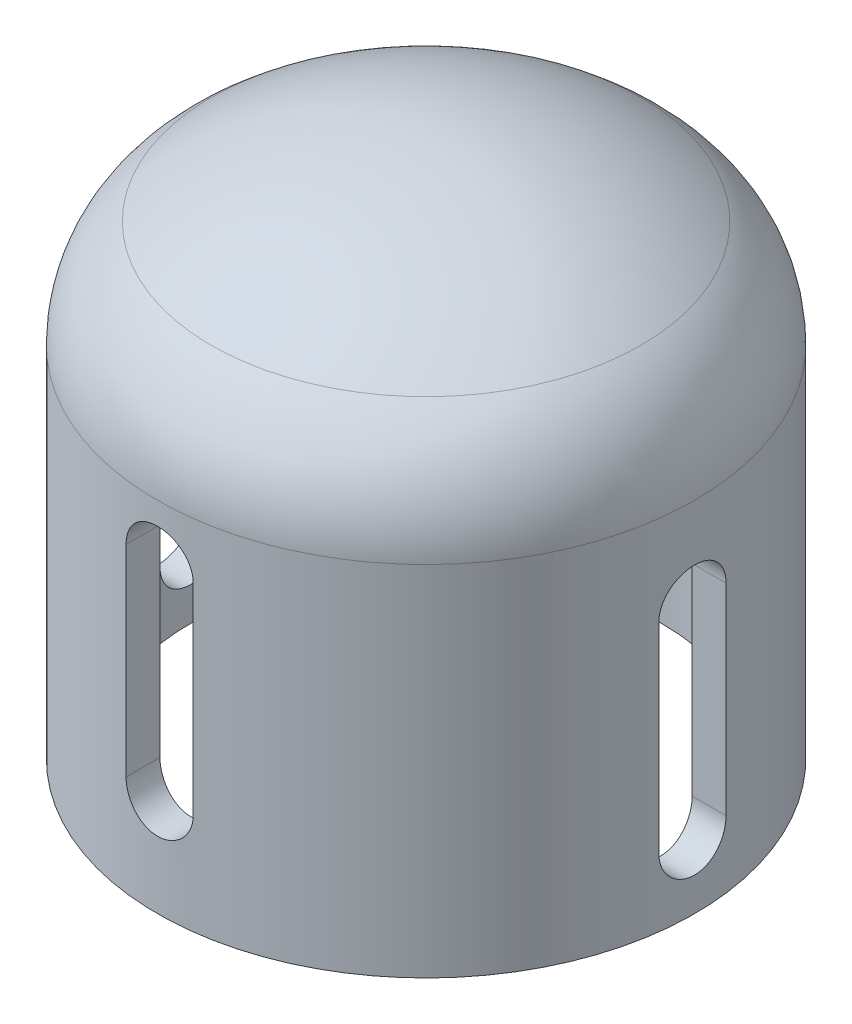
SolidWorks part; units mm, degrees
material "Acciaio inossidabile al cromo"
ref_plane "Piano frontale" through (0, 0, 0) normal (0, 0, 1) x (1, 0, 0)
ref_plane "Piano superiore" through (0, 0, 0) normal (0, 1, 0) x (1, 0, 0)
ref_plane "Piano destro" through (0, 0, 0) normal (1, 0, 0) x (0, 0, -1)
sketch "Schizzo1" plane through (0, 0, 0) normal (0, 0, 1) x (1, 0, 0)
  line L0 (0, 0) -> (0, 40) construction
  line L1 (20, 26.6667) -> (20, 0)
  line L4 (20, 0) -> (17.5, 0)
  line L5 (17.5, 0) -> (17.5, 27.863)
  line L6 (0, 40) -> (0, 37.5)
  arc A0 (0, 40) -> (16, 34.6667) centre (0, 13.3333) cw
  arc A1 (15.7609, 31.6533) -> (0, 37.5) centre (0, 13.3333) ccw
  arc A2 (16, 34.6667) -> (20, 26.6667) centre (10, 26.6667) cw
  arc A3 (17.5, 27.863) -> (15.7609, 31.6533) centre (12.5, 27.863) ccw
  point P7 (22.5, 0)
  point P11 (17.5, 27.2095)
  point P12 (22.5, 30.5771)
  point P13 (17.5, 27.598)
  point P14 (17.5, 30.5124)
  point P19 (17.5, 30)
  point P20 (22.5, 0.6337)
  dimension "D7" = 10
  dimension "D8" = 5
  dimension "D1" = 40
  dimension "D3" = 2.5
  dimension "D4" = 35
  dimension "D5" = 2.5
  dimension "D6" = 30
revolve "Rivoluzione1" add sketch "Schizzo1" angle 360 about L0
sketch "Schizzo2" plane through (0, 0, 0) normal (0, 0, 1) x (1, 0, 0)
  line L0 (0, 22.5) -> (0, 7.5) construction
  line L1 (2.5, 22.5) -> (2.5, 7.5)
  line L2 (-2.5, 22.5) -> (-2.5, 7.5)
  arc A0 (2.5, 22.5) -> (-2.5, 22.5) centre (0, 22.5) ccw
  arc A1 (-2.5, 7.5) -> (2.5, 7.5) centre (0, 7.5) ccw
  point P2 (0, 15)
  point P8 (0, 5)
  point P9 (2.0572, 23.3359)
  point P10 (0, 0)
  dimension "D1" = 5
  dimension "D2" = 15
  dimension "D3" = 5
extrude "Taglio-Estrusione1" cut sketch "Schizzo2" against normal through all both and the other way through all contours A1 L1 A0 L2
sketch "Schizzo3" plane through (0, 0, 0) normal (1, 0, 0) x (0, 0, -1)
  line L0 (0, 20) -> (0, 5) construction
  line L1 (2.5, 20) -> (2.5, 5)
  line L2 (-2.5, 20) -> (-2.5, 5)
  arc A0 (2.5, 20) -> (-2.5, 20) centre (0, 20) ccw
  arc A1 (-2.5, 5) -> (2.5, 5) centre (0, 5) ccw
  point P2 (0, 12.5)
  dimension "D1" = 5
  dimension "D2" = 5
  dimension "D3" = 15
extrude "Taglio-Estrusione2" cut sketch "Schizzo3" against normal through all both and the other way through all
